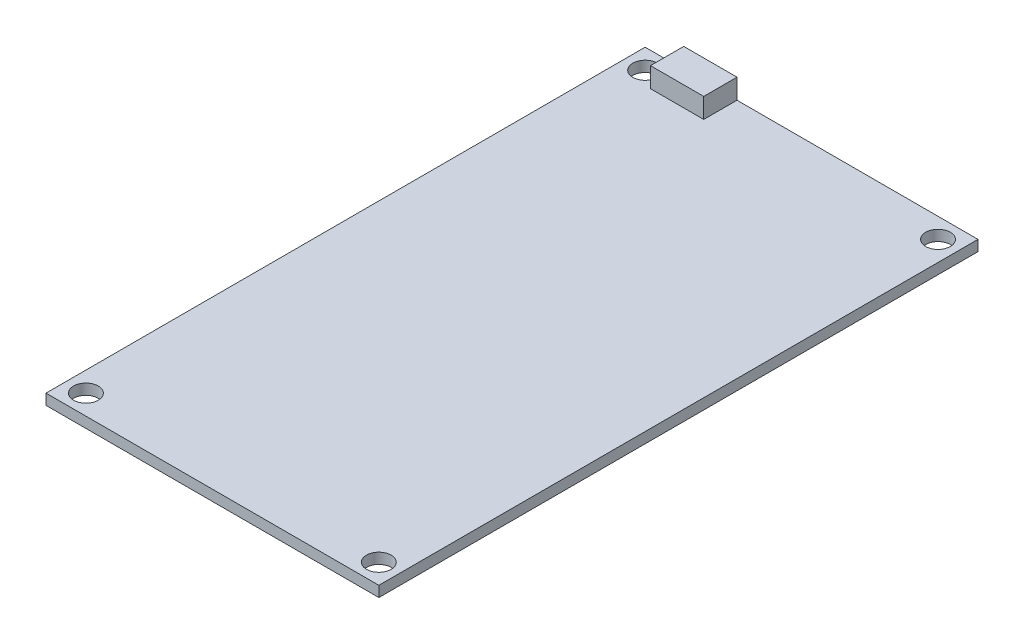
SolidWorks part; units mm, degrees
ref_plane "Front Plane" through (0, 0, 0) normal (0, 0, 1) x (1, 0, 0)
ref_plane "Top Plane" through (0, 0, 0) normal (0, 1, 0) x (1, 0, 0)
ref_plane "Right Plane" through (0, 0, 0) normal (1, 0, 0) x (0, 0, -1)
sketch "Sketch3" plane through (0, 0, 0) normal (0, 1, 0) x (1, 0, 0)
  line L1 (0, 0) -> (50, 0)
  line L2 (0, 0) -> (0, -90)
  line L3 (0, -90) -> (50, -90)
  line L4 (50, 0) -> (50, -90)
  dimension "D1" = 50
  dimension "D2" = 90
extrude "Boss-Extrude2" add sketch "Sketch3" along normal blind 1.6
sketch "Sketch4" plane through (0, 1.6, 0) normal (0, 1, 0) x (1, 0, 0)
  line L0 (0, 0) -> (0, -90) construction
  line L2 (50, 0) -> (0, 0) construction
  line L3 (0, -90) -> (50, -90) construction
  line L4 (50, -90) -> (50, 0) construction
  circle A0 centre (3, -3.0025) radius 1.854
  circle A1 centre (47, -3.0025) radius 1.854
  circle A2 centre (47, -87.0025) radius 1.854
  circle A3 centre (3, -87.0025) radius 1.854
  dimension "D1" = 3.708
  dimension "D2" = 3
  dimension "D3" = 3.0025
  dimension "D6" = 2.9975
  dimension "D7" = 3
  dimension "D8" = 3
  dimension "D4" = 2
  dimension "D5" = 2
extrude "Cut-Extrude1" cut sketch "Sketch4" against normal up to next
sketch "Sketch5" plane through (0, 1.6, 0) normal (0, 1, 0) x (1, 0, 0)
  line L0 (50, 0) -> (0, 0) construction
  line L1 (5.8, 0) -> (13.8, 0)
  line L2 (5.8, 0) -> (5.8, -5)
  line L3 (5.8, -5) -> (13.8, -5)
  line L4 (13.8, 0) -> (13.8, -5)
  line L5 (0, 0) -> (0, -90) construction
  dimension "D1" = 8
  dimension "D2" = 5
  dimension "D3" = 5.8
extrude "Boss-Extrude3" add sketch "Sketch5" along normal blind 3
